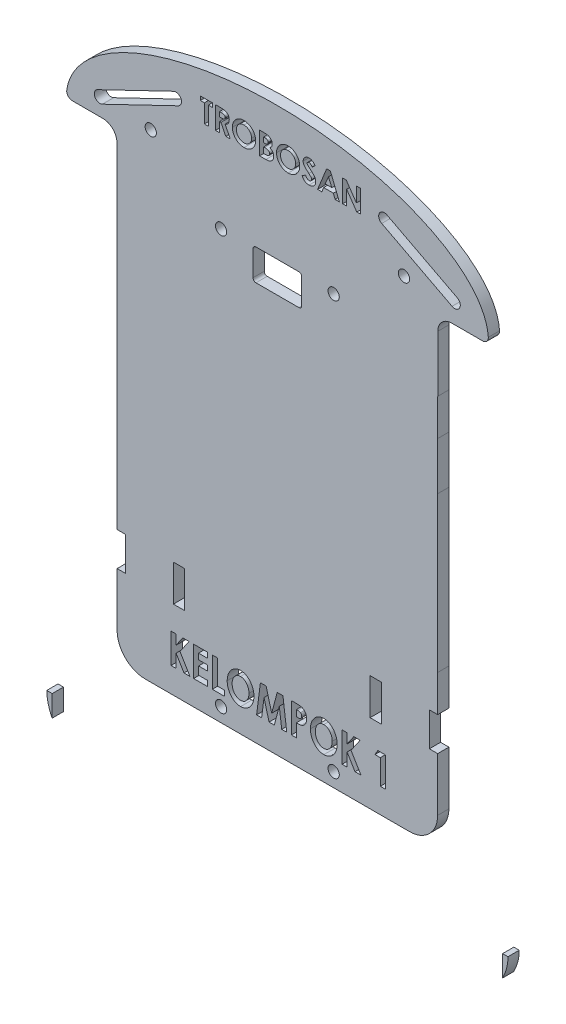
SolidWorks part; units mm, degrees
ref_plane "Front Plane" through (0, 0, 0) normal (0, 0, 1) x (1, 0, 0)
ref_plane "Top Plane" through (0, 0, 0) normal (0, 1, 0) x (1, 0, 0)
ref_plane "Right Plane" through (0, 0, 0) normal (1, 0, 0) x (0, 0, -1)
sketch "Sketch1" plane through (0, 0, 0) normal (0, 0, 1) x (1, 0, 0)
  line L0 (50.4961, 0) -> (-50.4961, 0) construction
  line L1 (0, 94) -> (0, -94) construction
  line L2 (-57, 93) -> (-57, 43.8389)
  line L3 (-56.98, 18) -> (-56.97, 18)
  line L4 (-56.97, 18) -> (-56.97, -18)
  line L5 (-56.97, -18) -> (-56.96, -18)
  line L6 (-56.96, -18) -> (-56.96, -31)
  line L8 (56.96, -18) -> (56.96, -31)
  line L9 (56.96, -18) -> (56.98, -18)
  line L10 (56.98, -18) -> (56.98, 37)
  line L11 (56.98, 37) -> (56.97, 37)
  line L12 (57, 92) -> (57, 67)
  line L13 (0, 94) -> (0, 138.6441) construction
  line L14 (-75, 93) -> (-57, 93)
  line L15 (57, 92) -> (74.9694, 92)
  line L16 (-81.95, -93) -> (-56.95, -93)
  line L17 (56.95, -93) -> (81.95, -93)
  line L18 (-57, 43.8389) -> (-56.99, 43.8393)
  line L19 (-56.99, 43.8393) -> (-56.99, 35)
  line L20 (-56.99, 35) -> (-56.98, 35)
  line L21 (-56.98, 35) -> (-56.98, 18)
  line L22 (57, 67) -> (56.99, 67)
  line L23 (56.99, 67) -> (56.99, 54)
  line L24 (56.99, 54) -> (56.97, 54)
  line L25 (56.97, 54) -> (56.97, 37)
  line L26 (-56.96, -31) -> (-54, -31)
  line L27 (-54, -43) -> (-56.95, -43)
  line L28 (-56.95, -43) -> (-56.95, -93)
  line L29 (-54, -31) -> (-54, -43)
  line L30 (-56.95, -93) -> (56.95, -93) construction
  line L31 (56.96, -31) -> (54, -31)
  line L32 (54, -31) -> (54, -43)
  line L33 (54, -43) -> (56.95, -43)
  line L34 (56.95, -43) -> (56.95, -93)
  circle A2 centre (0, 94) radius 10
  circle A3 centre (0, -94) radius 10
  circle A4 centre (0, 0) radius 1.9726
  ellipse E0 centre (0, 93) end of major axis (-75, 93) minor radius 35 (-75, 93) -> (74.9694, 92) cw
  ellipse E1 centre (0, -93) end of major axis (81.95, -93) minor radius 35 (-81.95, -93) -> (81.95, -93) ccw
  point P4 (0, 0)
  point P8 (0, 0)
  point P9 (0, 0)
  point P11 (0, 0)
  point P12 (0, 0)
  point P13 (0, 0)
  point P25 (0, 0)
  point P39 (0, -128)
  point P41 (0, 0)
  point P43 (0, 0)
  point P48 (0, 0)
  point P53 (-57, 93)
  point P54 (0, 0)
  point P57 (0, 0)
  point P62 (0, 0)
  point P67 (0, 0)
  point P68 (0, 0)
  point P69 (0, 0)
  point P70 (0, 0)
  point P71 (0, 0)
  point P72 (0, 0)
  point P73 (0, 0)
extrude "Boss-Extrude2" add sketch "Sketch1" along normal blind 4
sketch "Sketch25" plane through (0, 0, 0) normal (0, 0, -1) x (-1, 0, 0)
  line L1 (-30.9594, 48) -> (-30.9594, 34.3965) construction
  line L5 (-30.9594, 48) -> (-25.9623, 48)
  line L6 (-30.9594, 48) -> (-30.9594, 35.0074)
  line L7 (-30.9594, 35.0074) -> (-25.9623, 35.0074)
  line L8 (-25.9623, 48) -> (-25.9623, 35.0074)
  line L12 (25.0086, 48) -> (30.0057, 48)
  line L13 (25.0086, 48) -> (25.0086, 35.0074)
  line L14 (25.0086, 35.0074) -> (30.0057, 35.0074)
  line L15 (30.0057, 48) -> (30.0057, 35.0074)
  line L22 (-32.95, -31) -> (-36.9572, -31)
  line L23 (-32.95, -31) -> (-32.95, -43.9474)
  line L24 (-32.95, -43.9474) -> (-36.9572, -43.9474)
  line L25 (-36.9572, -31) -> (-36.9572, -43.9474)
  line L26 (36.9572, -31) -> (32.95, -31)
  line L27 (36.9572, -31) -> (36.9572, -43.9474)
  line L28 (36.9572, -43.9474) -> (32.95, -43.9474)
  line L29 (32.95, -31) -> (32.95, -43.9474)
  point P0 (0, 0)
  dimension "D2" = 4.9971
  dimension "D5" = 4.9971
  dimension "D7" = 4.0072
  dimension "D8" = 4.0072
extrude "Cut-Extrude25" cut sketch "Sketch25" against normal through all
sketch "Sketch28" plane through (0, 0, 0) normal (0, 0, -1) x (-1, 0, 0)
  line L1 (30, -112) -> (-30, -112)
  line L2 (-30, 112) -> (30, 112) construction
  line L3 (-30, 114) -> (30, 114)
  line L4 (-30, 110) -> (30, 110)
  line L5 (-30, -112) -> (30, -112) construction
  line L6 (-30, -110) -> (30, -110)
  line L7 (-30, -114) -> (30, -114)
  line L8 (-63, 99) -> (-38, 112) construction
  line L9 (-63.9227, 100.7744) -> (-38.9227, 113.7744)
  line L10 (-62.0773, 97.2256) -> (-37.0773, 110.2256)
  line L11 (36.0632, 112.09) -> (63.0485, 99.1007) construction
  line L12 (36.9306, 113.8921) -> (63.9159, 100.9028)
  line L13 (35.1957, 110.2879) -> (62.1811, 97.2986)
  line L21 (36, -112) -> (63, -99) construction
  line L22 (35.1324, -110.198) -> (62.1324, -97.198)
  line L23 (36.8676, -113.802) -> (63.8676, -100.802)
  line L24 (-63, -99) -> (-38, -112.1208) construction
  line L25 (-62.0706, -97.2291) -> (-37.0706, -110.3499)
  line L26 (-63.9294, -100.7709) -> (-38.9294, -113.8918)
  arc A0 (-30, 114) -> (-30, 110) centre (-30, 112) ccw
  arc A1 (30, 110) -> (30, 114) centre (30, 112) ccw
  arc A2 (-63.9227, 100.7744) -> (-62.0773, 97.2256) centre (-63, 99) ccw
  arc A4 (-37.0773, 110.2256) -> (-38.9227, 113.7744) centre (-38, 112) ccw
  arc A5 (36.9306, 113.8921) -> (35.1957, 110.2879) centre (36.0632, 112.09) ccw
  arc A6 (62.1811, 97.2986) -> (63.9159, 100.9028) centre (63.0485, 99.1007) ccw
  arc A7 (35.1324, -110.198) -> (36.8676, -113.802) centre (36, -112) ccw
  arc A8 (-30, -110) -> (-30, -114) centre (-30, -112) ccw
  arc A9 (30, -114) -> (30, -110) centre (30, -112) ccw
  arc A11 (63.8676, -100.802) -> (62.1324, -97.198) centre (63, -99) ccw
  arc A12 (-62.0706, -97.2291) -> (-63.9294, -100.7709) centre (-63, -99) ccw
  arc A13 (-38.9294, -113.8918) -> (-37.0706, -110.3499) centre (-38, -112.1208) ccw
  point P4 (0, -112)
  point P6 (0, -112)
  point P10 (0, 112)
  point P15 (-36, -112)
  point P16 (0, -112)
  point P22 (-30, -112)
  point P23 (-38, -112.1208)
  point P25 (63.0485, 99.1007)
  point P26 (-38, 112)
  point P29 (-50.5, 105.5)
  point P35 (34, -112)
  point P36 (36.0632, 112.09)
  point P39 (49.5558, 105.5954)
  point P44 (30, -112)
  point P57 (36, -112)
  point P60 (49.5, -105.5)
  point P65 (-50.5, -105.5604)
extrude "Cut-Extrude29" cut sketch "Sketch28" against normal through all contours L9 A4 L10 A2 | L3 A1 L4 A0 | L12 A6 L13 A5 | L26 A13 L25 A12 | L7 A9 L6 A8 | L23 A11 L22 A7
sketch "Sketch33" plane through (0, 0, 0) normal (0, 0, -1) x (-1, 0, 0)
  line L1 (-12.8608, 105.0896) -> (12.8076, 105.0896)
  line L2 (-12.8608, 105.0896) -> (-12.8608, 83.2737)
  line L3 (-12.8608, 83.2737) -> (12.8076, 83.2737)
  line L4 (12.8076, 105.0896) -> (12.8076, 83.2737)
extrude "Boss-Extrude6" add sketch "Sketch33" against normal blind 4
sketch "Sketch34" plane through (0, 0, 4) normal (0, 0, 1) x (1, 0, 0)
  line L1 (-50, 50) -> (50, 50)
  line L2 (-50, 50) -> (-50, 34.3734)
  line L3 (-50, 34.3734) -> (50, 34.3734)
  line L4 (50, 50) -> (50, 34.3734)
extrude "Boss-Extrude8" add sketch "Sketch34" against normal blind 4
sketch "Sketch35" plane through (0, 0, 4) normal (0, 0, 1) x (1, 0, 0)
  line L1 (-4.2047, 3.8705) -> (3.3615, 3.8705)
  line L2 (-4.2047, 3.8705) -> (-4.2047, -3.8104)
  line L3 (-4.2047, -3.8104) -> (3.3615, -3.8104)
  line L4 (3.3615, 3.8705) -> (3.3615, -3.8104)
extrude "Boss-Extrude9" add sketch "Sketch35" against normal blind 4
sketch "Sketch42" plane through (0, 0, 4) normal (0, 0, 1) x (1, 0, 0)
  line L1 (-33.2628, 115.9037) -> (33.3138, 115.9037)
  line L2 (-33.2628, 115.9037) -> (-33.2628, 108.319)
  line L3 (-33.2628, 108.319) -> (33.3138, 108.319)
  line L4 (33.3138, 115.9037) -> (33.3138, 108.319)
extrude "Boss-Extrude12" add sketch "Sketch42" against normal blind 4
sketch "Sketch43" plane through (0, 0, 4) normal (0, 0, 1) x (1, 0, 0)
  line L1 (-80.0131, -72) -> (80.041, -72)
  line L2 (-80.0131, -72) -> (-80.0131, -132.0859)
  line L3 (-80.0131, -132.0859) -> (80.041, -132.0859)
  line L4 (80.041, -72) -> (80.041, -132.0859)
extrude "Cut-Extrude33" cut sketch "Sketch43" against normal blind 4
fillet "Fillet2" radius 10 1 edges at (56.95, -72, 2)
fillet "Fillet3" radius 10 1 edges at (-56.95, -72, 2)
sketch "Sketch45" plane through (0, 0, 4) normal (0, 0, 1) x (1, 0, 0)
  text T0 "TROBOSAN" font "Century Gothic" height in points 30
extrude "Cut-Extrude34" cut sketch "Sketch45" against normal blind 4
sketch "Sketch48" plane through (0, 0, 4) normal (0, 0, 1) x (1, 0, 0)
  line L1 (-31.0624, 107.058) -> (-30.1532, 107.058)
  line L2 (-31.0624, 107.058) -> (-31.0624, 118.943)
  line L3 (-31.0624, 118.943) -> (-30.1532, 118.943)
  line L4 (-30.1532, 107.058) -> (-30.1532, 118.943)
extrude "Boss-Extrude23" add sketch "Sketch48" against normal blind 4
sketch "Sketch55" plane through (0, 0, 4) normal (0, 0, 1) x (1, 0, 0)
  line L1 (-9.1573, 103.6676) -> (-8.1537, 103.6676)
  line L2 (-9.1573, 103.6676) -> (-9.1573, 92.2474)
  line L3 (-9.1573, 92.2474) -> (-8.1537, 92.2474)
  line L4 (-8.1537, 103.6676) -> (-8.1537, 92.2474)
extrude "Boss-Extrude24" add sketch "Sketch55" against normal blind 4
sketch "Sketch56" plane through (0, 0, 4) normal (0, 0, 1) x (1, 0, 0)
  line L1 (-19.2633, 104.2479) -> (-18.0661, 104.2479)
  line L2 (-19.2633, 104.2479) -> (-19.2633, 91.6865)
  line L3 (-19.2633, 91.6865) -> (-18.0661, 91.6865)
  line L4 (-18.0661, 104.2479) -> (-18.0661, 91.6865)
extrude "Boss-Extrude25" add sketch "Sketch56" against normal blind 4
sketch "Sketch57" plane through (0, 0, 4) normal (0, 0, 1) x (1, 0, 0)
  line L1 (2.6551, 101.2511) -> (3.8655, 101.2511)
  line L2 (2.6551, 101.2511) -> (2.6551, 87.9834)
  line L3 (2.6551, 87.9834) -> (3.8655, 87.9834)
  line L4 (3.8655, 101.2511) -> (3.8655, 87.9834)
extrude "Boss-Extrude26" add sketch "Sketch57" against normal blind 4
sketch "Sketch62" plane through (0, 0, 4) normal (0, 0, 1) x (1, 0, 0)
  line L0 (19.7899, 93.372) -> (24.1136, 104.8409)
extrude "Extrude-Thin6" add sketch "Sketch62" against normal blind 4 thin thin type one direction wall 1
sketch "Sketch63" plane through (0, 0, 4) normal (0, 0, 1) x (1, 0, 0)
  circle A0 centre (20, 80) radius 2
extrude "Cut-Extrude35" cut sketch "Sketch63" against normal blind 4
sketch "Sketch64" plane through (0, 0, 4) normal (0, 0, 1) x (1, 0, 0)
  circle A0 centre (-20, 80) radius 2
extrude "Cut-Extrude36" cut sketch "Sketch64" against normal blind 4
fillet "Fillet4" radius 5 1 edges at (-57, 93, 2)
fillet "Fillet5" radius 5 1 edges at (57, 92, 2)
fillet "Fillet6" radius 2 3 edges at (1.0715, 127.9964, 0) (74.9694, 92, 2) (1.0715, 127.9964, 4)
fillet "Fillet7" radius 2 1 edges at (-75, 93, 2)
sketch "Sketch65" plane through (0, 0, 4) normal (0, 0, 1) x (1, 0, 0)
  text T0 "KELOMPOK 1" font "Century Gothic" height in points 40
extrude "Cut-Extrude37" cut sketch "Sketch65" against normal blind 10
sketch "Sketch66" plane through (0, 0, 4) normal (0, 0, 1) x (1, 0, 0)
  circle A0 centre (-45, 98) radius 2
extrude "Cut-Extrude38" cut sketch "Sketch66" against normal blind 10
sketch "Sketch67" plane through (0, 0, 4) normal (0, 0, 1) x (1, 0, 0)
  circle A0 centre (45, 98) radius 2
extrude "Cut-Extrude39" cut sketch "Sketch67" against normal blind 10
sketch "Sketch68" plane through (0, 0, 4) normal (0, 0, 1) x (1, 0, 0)
  circle A0 centre (-20, -67) radius 2
extrude "Cut-Extrude40" cut sketch "Sketch68" against normal blind 10
sketch "Sketch69" plane through (0, 0, 4) normal (0, 0, 1) x (1, 0, 0)
  circle A0 centre (20, -67) radius 2
extrude "Cut-Extrude41" cut sketch "Sketch69" against normal blind 10
sketch "Sketch70" plane through (0, 0, 4) normal (0, 0, 1) x (1, 0, 0)
  line L1 (-13.5939, -34.2924) -> (-12.6198, -34.2924)
  line L2 (-13.5939, -34.2924) -> (-13.5939, -47.1507)
  line L3 (-13.5939, -47.1507) -> (-12.6198, -47.1507)
  line L4 (-12.6198, -34.2924) -> (-12.6198, -47.1507)
extrude "Boss-Extrude27" add sketch "Sketch70" against normal blind 4
sketch "Sketch71" plane through (0, 0, 4) normal (0, 0, 1) x (1, 0, 0)
  line L1 (6.6396, -33.2761) -> (7.4437, -33.2761)
  line L2 (6.6396, -33.2761) -> (6.6396, -47.1397)
  line L3 (6.6396, -47.1397) -> (7.4437, -47.1397)
  line L4 (7.4437, -33.2761) -> (7.4437, -47.1397)
extrude "Boss-Extrude28" add sketch "Sketch71" against normal blind 4
sketch "Sketch72" plane through (0, 0, 4) normal (0, 0, 1) x (1, 0, 0)
  line L1 (15.9733, -35.9821) -> (17.0016, -35.9821)
  line L2 (15.9733, -35.9821) -> (15.9733, -48.622)
  line L3 (15.9733, -48.622) -> (17.0016, -48.622)
  line L4 (17.0016, -35.9821) -> (17.0016, -48.622)
extrude "Boss-Extrude29" add sketch "Sketch72" against normal blind 4
sketch "Sketch73" plane through (0, 0, 4) normal (0, 0, 1) x (1, 0, 0)
  line L1 (-8.65, 80.647) -> (8.65, 80.647)
  line L2 (-8.65, 80.647) -> (-8.65, 69.6156)
  line L3 (-8.65, 69.6156) -> (8.65, 69.6156)
  line L4 (8.65, 80.647) -> (8.65, 69.6156)
extrude "Cut-Extrude42" cut sketch "Sketch73" against normal blind 10
fillet "Fillet9" radius 1.04 1 edges at (8.65, 80.647, 2)
fillet "Fillet10" radius 1.04 1 edges at (-8.65, 80.647, 2)
fillet "Fillet11" radius 1.04 1 edges at (8.65, 69.6156, 2)
fillet "Fillet12" radius 1.04 1 edges at (-8.65, 69.6156, 2)
